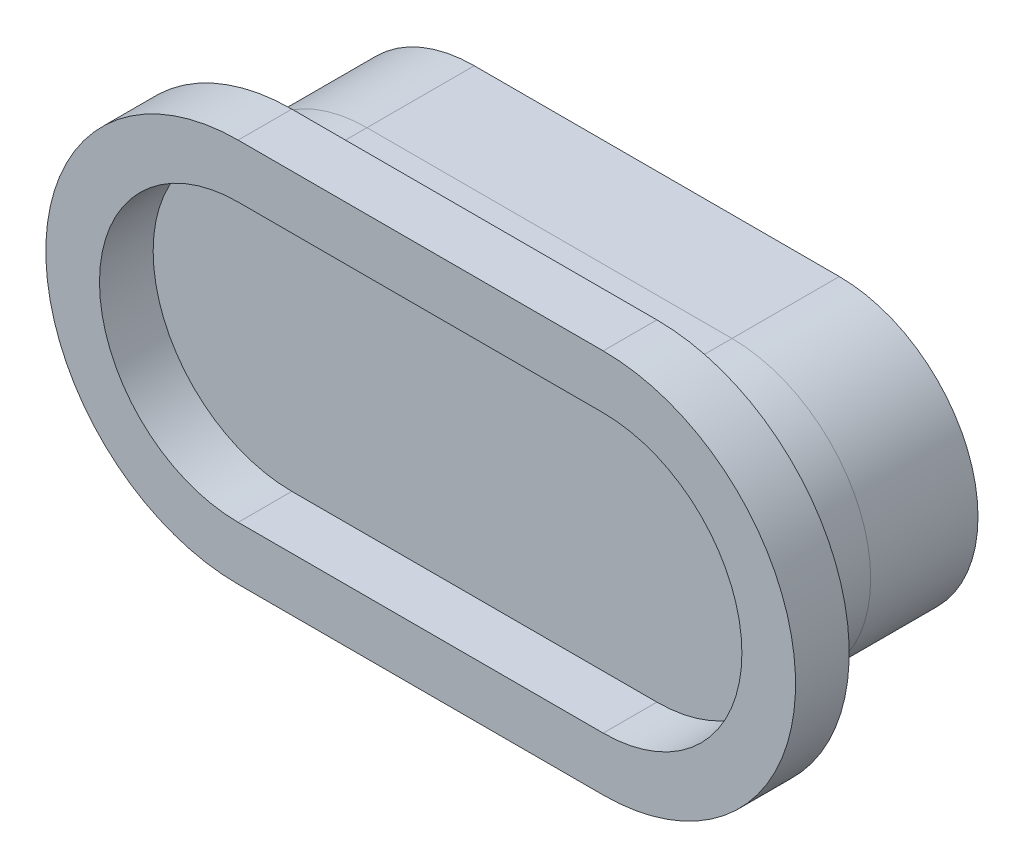
SolidWorks part; units mm, degrees
ref_plane "前视基准面" through (0, 0, 0) normal (0, 0, 1) x (1, 0, 0)
ref_plane "上视基准面" through (0, 0, 0) normal (0, 1, 0) x (1, 0, 0)
ref_plane "右视基准面" through (0, 0, 0) normal (1, 0, 0) x (0, 0, -1)
other "Configuration Table"
sketch "草图1" plane through (0, 0, 0) normal (0, 0, 1) x (1, 0, 0)
  line L0 (0, 0) -> (68.0282, 0) construction
  line L1 (0, 25.8454) -> (68.0282, 25.8454)
  line L2 (0, -25.8454) -> (68.0282, -25.8454)
  arc A0 (0, 25.8454) -> (0, -25.8454) centre (0, 0) ccw
  arc A1 (68.0282, -25.8454) -> (68.0282, 25.8454) centre (68.0282, 0) ccw
  point P3 (34.0141, 0)
extrude "凸台-拉伸1" add sketch "草图1" along normal blind 20 contours L2 A1 L1 A0
sketch "草图4" plane through (0, 0, 20) normal (0, 0, 1) x (1, 0, 0)
sketch "草图5" plane through (0, 0, 20) normal (0, 0, 1) x (1, 0, 0)
sketch "草图6" plane through (0, 0, 20) normal (0, 0, 1) x (1, 0, 0)
  line L2 (0, -25.8454) -> (68.0282, -25.8454)
  line L3 (68.0282, 25.8454) -> (0, 25.8454)
  line L4 (0, -25.8454) -> (68.0282, -25.8454)
  line L5 (68.0282, 25.8454) -> (0, 25.8454)
  arc A2 (0, 25.8454) -> (0, -25.8454) centre (0, 0) ccw
  arc A3 (68.0282, -25.8454) -> (68.0282, 25.8454) centre (68.0282, 0) ccw
  arc A4 (0, 25.8454) -> (0, -25.8454) centre (0, 0) ccw
  arc A5 (68.0282, -25.8454) -> (68.0282, 25.8454) centre (68.0282, 0) ccw
  dimension "D1" = 0
extrude "凸台-拉伸2" add sketch "草图6" along normal blind 14 separate body contours A4 L4 A5 L5
sketch "草图7" plane through (0, 0, 34) normal (0, 0, 1) x (1, 0, 0)
  line L2 (68.0282, 25.8454) -> (0, 25.8454)
  line L3 (0, -25.8454) -> (68.0282, -25.8454)
  line L4 (68.0282, 25.8454) -> (0, 25.8454)
  line L5 (0, -25.8454) -> (68.0282, -25.8454)
  arc A2 (0, 25.8454) -> (0, -25.8454) centre (0, 0) ccw
  arc A3 (68.0282, -25.8454) -> (68.0282, 25.8454) centre (68.0282, 0) ccw
  arc A4 (0, 25.8454) -> (0, -25.8454) centre (0, 0) ccw
  arc A5 (68.0282, -25.8454) -> (68.0282, 25.8454) centre (68.0282, 0) ccw
  dimension "D1" = 0
extrude "拉伸-薄壁1" add sketch "草图7" along normal blind 10 separate body thin contours L4 A4 L5 A5
